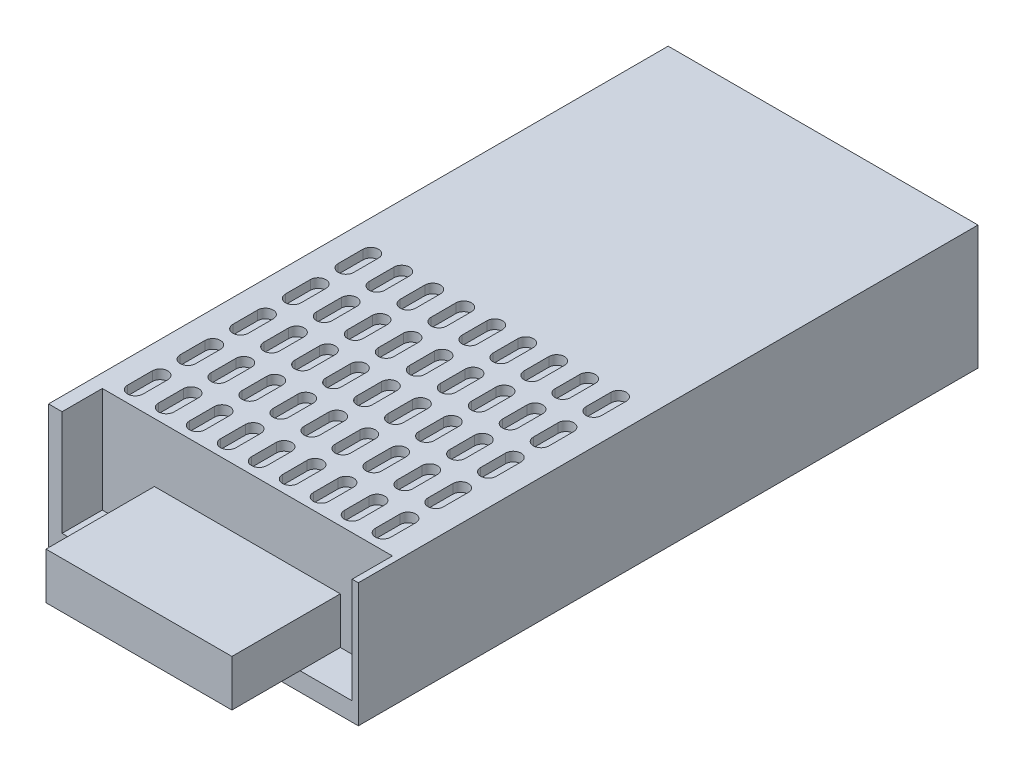
SolidWorks part; units mm, degrees
ref_plane "Front Plane" through (0, 0, 0) normal (0, 0, 1) x (1, 0, 0)
ref_plane "Top Plane" through (0, 0, 0) normal (0, 1, 0) x (1, 0, 0)
ref_plane "Right Plane" through (0, 0, 0) normal (1, 0, 0) x (0, 0, -1)
sketch "Sketch1" plane through (0, 0, 0) normal (0, 0, 1) x (1, 0, 0)
  line L1 (0, 0) -> (100, 0)
  line L2 (0, 0) -> (0, 40)
  line L3 (0, 40) -> (100, 40)
  line L4 (100, 0) -> (100, 40)
  dimension "D1" = 100
  dimension "D2" = 40
extrude "Boss-Extrude1" add sketch "Sketch1" along normal blind 200
sketch "Sketch2" plane through (0, 40, 0) normal (0, 1, 0) x (1, 0, 0)
  line L0 (100, -200) -> (0, -200) construction
  line L1 (4.3642, -200) -> (98, -200)
  line L2 (4.3642, -200) -> (4.3642, -187)
  line L3 (4.3642, -187) -> (98, -187)
  line L4 (98, -200) -> (98, -187)
  line L5 (100, -200) -> (100, 0) construction
  dimension "D1" = 13
  dimension "D2" = 2
extrude "Cut-Extrude1" cut sketch "Sketch2" against normal blind 34
sketch "Sketch3" plane through (0, 0, 187) normal (0, 0, 1) x (1, 0, 0)
  line L0 (98, 6) -> (4.3642, 6) construction
  line L1 (21.1821, 6) -> (81.1821, 6)
  line L2 (21.1821, 6) -> (21.1821, 21)
  line L3 (21.1821, 21) -> (81.1821, 21)
  line L4 (81.1821, 6) -> (81.1821, 21)
  line L5 (4.3642, 6) -> (98, 6) construction
  point P8 (51.1821, 6)
  point P9 (51.1821, 6)
  dimension "D1" = 60
  dimension "D2" = 15
extrude "Boss-Extrude2" add sketch "Sketch3" along normal blind 35
sketch "Sketch4" plane through (0, 40, 0) normal (0, 1, 0) x (1, 0, 0)
  line L0 (0, -200) -> (0, 0) construction
  line L2 (7.5, -174) -> (7.5, -182)
  line L4 (12.5, -174) -> (12.5, -182)
  line L5 (98, -187) -> (4.3642, -187) construction
  line L6 (17.5, -174) -> (17.5, -182)
  line L7 (22.5, -174) -> (22.5, -182)
  line L8 (27.5, -174) -> (27.5, -182)
  line L9 (32.5, -174) -> (32.5, -182)
  line L10 (37.5, -174) -> (37.5, -182)
  line L11 (42.5, -174) -> (42.5, -182)
  line L12 (47.5, -174) -> (47.5, -182)
  line L13 (52.5, -174) -> (52.5, -182)
  line L14 (57.5, -174) -> (57.5, -182)
  line L15 (62.5, -174) -> (62.5, -182)
  line L16 (67.5, -174) -> (67.5, -182)
  line L17 (72.5, -174) -> (72.5, -182)
  line L18 (77.5, -174) -> (77.5, -182)
  line L19 (82.5, -174) -> (82.5, -182)
  line L20 (87.5, -174) -> (87.5, -182)
  line L21 (92.5, -174) -> (92.5, -182)
  line L22 (17.5, -157) -> (17.5, -165)
  line L23 (22.5, -157) -> (22.5, -165)
  line L24 (27.5, -157) -> (27.5, -165)
  line L25 (32.5, -157) -> (32.5, -165)
  line L26 (37.5, -157) -> (37.5, -165)
  line L27 (42.5, -157) -> (42.5, -165)
  line L28 (47.5, -157) -> (47.5, -165)
  line L29 (52.5, -157) -> (52.5, -165)
  line L30 (57.5, -157) -> (57.5, -165)
  line L31 (62.5, -157) -> (62.5, -165)
  line L32 (67.5, -157) -> (67.5, -165)
  line L33 (72.5, -157) -> (72.5, -165)
  line L34 (77.5, -157) -> (77.5, -165)
  line L35 (82.5, -157) -> (82.5, -165)
  line L36 (87.5, -157) -> (87.5, -165)
  line L37 (92.5, -157) -> (92.5, -165)
  line L38 (17.5, -140) -> (17.5, -148)
  line L39 (22.5, -140) -> (22.5, -148)
  line L40 (27.5, -140) -> (27.5, -148)
  line L41 (32.5, -140) -> (32.5, -148)
  line L42 (37.5, -140) -> (37.5, -148)
  line L43 (42.5, -140) -> (42.5, -148)
  line L44 (47.5, -140) -> (47.5, -148)
  line L45 (52.5, -140) -> (52.5, -148)
  line L46 (57.5, -140) -> (57.5, -148)
  line L47 (62.5, -140) -> (62.5, -148)
  line L48 (67.5, -140) -> (67.5, -148)
  line L49 (72.5, -140) -> (72.5, -148)
  line L50 (77.5, -140) -> (77.5, -148)
  line L51 (82.5, -140) -> (82.5, -148)
  line L52 (87.5, -140) -> (87.5, -148)
  line L53 (92.5, -140) -> (92.5, -148)
  line L54 (17.5, -123) -> (17.5, -131)
  line L55 (22.5, -123) -> (22.5, -131)
  line L56 (27.5, -123) -> (27.5, -131)
  line L57 (32.5, -123) -> (32.5, -131)
  line L58 (37.5, -123) -> (37.5, -131)
  line L59 (42.5, -123) -> (42.5, -131)
  line L60 (47.5, -123) -> (47.5, -131)
  line L61 (52.5, -123) -> (52.5, -131)
  line L62 (57.5, -123) -> (57.5, -131)
  line L63 (62.5, -123) -> (62.5, -131)
  line L64 (67.5, -123) -> (67.5, -131)
  line L65 (72.5, -123) -> (72.5, -131)
  line L66 (77.5, -123) -> (77.5, -131)
  line L67 (82.5, -123) -> (82.5, -131)
  line L68 (87.5, -123) -> (87.5, -131)
  line L69 (92.5, -123) -> (92.5, -131)
  line L70 (17.5, -106) -> (17.5, -114)
  line L71 (22.5, -106) -> (22.5, -114)
  line L72 (27.5, -106) -> (27.5, -114)
  line L73 (32.5, -106) -> (32.5, -114)
  line L74 (37.5, -106) -> (37.5, -114)
  line L75 (42.5, -106) -> (42.5, -114)
  line L76 (47.5, -106) -> (47.5, -114)
  line L77 (52.5, -106) -> (52.5, -114)
  line L78 (57.5, -106) -> (57.5, -114)
  line L79 (62.5, -106) -> (62.5, -114)
  line L80 (67.5, -106) -> (67.5, -114)
  line L81 (72.5, -106) -> (72.5, -114)
  line L82 (77.5, -106) -> (77.5, -114)
  line L83 (82.5, -106) -> (82.5, -114)
  line L84 (87.5, -106) -> (87.5, -114)
  line L85 (92.5, -106) -> (92.5, -114)
  line L86 (7.5, -157) -> (7.5, -165)
  line L87 (12.5, -157) -> (12.5, -165)
  line L88 (7.5, -140) -> (7.5, -148)
  line L89 (12.5, -140) -> (12.5, -148)
  line L90 (7.5, -123) -> (7.5, -131)
  line L91 (12.5, -123) -> (12.5, -131)
  line L92 (7.5, -106) -> (7.5, -114)
  line L93 (12.5, -106) -> (12.5, -114)
  arc A0 (12.5, -174) -> (7.5, -174) centre (10, -174) ccw
  arc A1 (7.5, -182) -> (12.5, -182) centre (10, -182) ccw
  arc A2 (22.5, -174) -> (17.5, -174) centre (20, -174) ccw
  arc A3 (17.5, -182) -> (22.5, -182) centre (20, -182) ccw
  arc A4 (32.5, -174) -> (27.5, -174) centre (30, -174) ccw
  arc A5 (27.5, -182) -> (32.5, -182) centre (30, -182) ccw
  arc A6 (42.5, -174) -> (37.5, -174) centre (40, -174) ccw
  arc A7 (37.5, -182) -> (42.5, -182) centre (40, -182) ccw
  arc A8 (52.5, -174) -> (47.5, -174) centre (50, -174) ccw
  arc A9 (47.5, -182) -> (52.5, -182) centre (50, -182) ccw
  arc A10 (62.5, -174) -> (57.5, -174) centre (60, -174) ccw
  arc A11 (57.5, -182) -> (62.5, -182) centre (60, -182) ccw
  arc A12 (72.5, -174) -> (67.5, -174) centre (70, -174) ccw
  arc A13 (67.5, -182) -> (72.5, -182) centre (70, -182) ccw
  arc A14 (82.5, -174) -> (77.5, -174) centre (80, -174) ccw
  arc A15 (77.5, -182) -> (82.5, -182) centre (80, -182) ccw
  arc A16 (92.5, -174) -> (87.5, -174) centre (90, -174) ccw
  arc A17 (87.5, -182) -> (92.5, -182) centre (90, -182) ccw
  arc A18 (22.5, -157) -> (17.5, -157) centre (20, -157) ccw
  arc A19 (17.5, -165) -> (22.5, -165) centre (20, -165) ccw
  arc A20 (32.5, -157) -> (27.5, -157) centre (30, -157) ccw
  arc A21 (27.5, -165) -> (32.5, -165) centre (30, -165) ccw
  arc A22 (42.5, -157) -> (37.5, -157) centre (40, -157) ccw
  arc A23 (37.5, -165) -> (42.5, -165) centre (40, -165) ccw
  arc A24 (52.5, -157) -> (47.5, -157) centre (50, -157) ccw
  arc A25 (47.5, -165) -> (52.5, -165) centre (50, -165) ccw
  arc A26 (62.5, -157) -> (57.5, -157) centre (60, -157) ccw
  arc A27 (57.5, -165) -> (62.5, -165) centre (60, -165) ccw
  arc A28 (72.5, -157) -> (67.5, -157) centre (70, -157) ccw
  arc A29 (67.5, -165) -> (72.5, -165) centre (70, -165) ccw
  arc A30 (82.5, -157) -> (77.5, -157) centre (80, -157) ccw
  arc A31 (77.5, -165) -> (82.5, -165) centre (80, -165) ccw
  arc A32 (92.5, -157) -> (87.5, -157) centre (90, -157) ccw
  arc A33 (87.5, -165) -> (92.5, -165) centre (90, -165) ccw
  arc A34 (22.5, -140) -> (17.5, -140) centre (20, -140) ccw
  arc A35 (17.5, -148) -> (22.5, -148) centre (20, -148) ccw
  arc A36 (32.5, -140) -> (27.5, -140) centre (30, -140) ccw
  arc A37 (27.5, -148) -> (32.5, -148) centre (30, -148) ccw
  arc A38 (42.5, -140) -> (37.5, -140) centre (40, -140) ccw
  arc A39 (37.5, -148) -> (42.5, -148) centre (40, -148) ccw
  arc A40 (52.5, -140) -> (47.5, -140) centre (50, -140) ccw
  arc A41 (47.5, -148) -> (52.5, -148) centre (50, -148) ccw
  arc A42 (62.5, -140) -> (57.5, -140) centre (60, -140) ccw
  arc A43 (57.5, -148) -> (62.5, -148) centre (60, -148) ccw
  arc A44 (72.5, -140) -> (67.5, -140) centre (70, -140) ccw
  arc A45 (67.5, -148) -> (72.5, -148) centre (70, -148) ccw
  arc A46 (82.5, -140) -> (77.5, -140) centre (80, -140) ccw
  arc A47 (77.5, -148) -> (82.5, -148) centre (80, -148) ccw
  arc A48 (92.5, -140) -> (87.5, -140) centre (90, -140) ccw
  arc A49 (87.5, -148) -> (92.5, -148) centre (90, -148) ccw
  arc A50 (22.5, -123) -> (17.5, -123) centre (20, -123) ccw
  arc A51 (17.5, -131) -> (22.5, -131) centre (20, -131) ccw
  arc A52 (32.5, -123) -> (27.5, -123) centre (30, -123) ccw
  arc A53 (27.5, -131) -> (32.5, -131) centre (30, -131) ccw
  arc A54 (42.5, -123) -> (37.5, -123) centre (40, -123) ccw
  arc A55 (37.5, -131) -> (42.5, -131) centre (40, -131) ccw
  arc A56 (52.5, -123) -> (47.5, -123) centre (50, -123) ccw
  arc A57 (47.5, -131) -> (52.5, -131) centre (50, -131) ccw
  arc A58 (62.5, -123) -> (57.5, -123) centre (60, -123) ccw
  arc A59 (57.5, -131) -> (62.5, -131) centre (60, -131) ccw
  arc A60 (72.5, -123) -> (67.5, -123) centre (70, -123) ccw
  arc A61 (67.5, -131) -> (72.5, -131) centre (70, -131) ccw
  arc A62 (82.5, -123) -> (77.5, -123) centre (80, -123) ccw
  arc A63 (77.5, -131) -> (82.5, -131) centre (80, -131) ccw
  arc A64 (92.5, -123) -> (87.5, -123) centre (90, -123) ccw
  arc A65 (87.5, -131) -> (92.5, -131) centre (90, -131) ccw
  arc A66 (22.5, -106) -> (17.5, -106) centre (20, -106) ccw
  arc A67 (17.5, -114) -> (22.5, -114) centre (20, -114) ccw
  arc A68 (32.5, -106) -> (27.5, -106) centre (30, -106) ccw
  arc A69 (27.5, -114) -> (32.5, -114) centre (30, -114) ccw
  arc A70 (42.5, -106) -> (37.5, -106) centre (40, -106) ccw
  arc A71 (37.5, -114) -> (42.5, -114) centre (40, -114) ccw
  arc A72 (52.5, -106) -> (47.5, -106) centre (50, -106) ccw
  arc A73 (47.5, -114) -> (52.5, -114) centre (50, -114) ccw
  arc A74 (62.5, -106) -> (57.5, -106) centre (60, -106) ccw
  arc A75 (57.5, -114) -> (62.5, -114) centre (60, -114) ccw
  arc A76 (72.5, -106) -> (67.5, -106) centre (70, -106) ccw
  arc A77 (67.5, -114) -> (72.5, -114) centre (70, -114) ccw
  arc A78 (82.5, -106) -> (77.5, -106) centre (80, -106) ccw
  arc A79 (77.5, -114) -> (82.5, -114) centre (80, -114) ccw
  arc A80 (92.5, -106) -> (87.5, -106) centre (90, -106) ccw
  arc A81 (87.5, -114) -> (92.5, -114) centre (90, -114) ccw
  arc A82 (12.5, -157) -> (7.5, -157) centre (10, -157) ccw
  arc A83 (7.5, -165) -> (12.5, -165) centre (10, -165) ccw
  arc A84 (12.5, -140) -> (7.5, -140) centre (10, -140) ccw
  arc A85 (7.5, -148) -> (12.5, -148) centre (10, -148) ccw
  arc A86 (12.5, -123) -> (7.5, -123) centre (10, -123) ccw
  arc A87 (7.5, -131) -> (12.5, -131) centre (10, -131) ccw
  arc A88 (12.5, -106) -> (7.5, -106) centre (10, -106) ccw
  arc A89 (7.5, -114) -> (12.5, -114) centre (10, -114) ccw
  dimension "D1" = 8
  dimension "D2" = 5
  dimension "D3" = 10
  dimension "D4" = 5
  dimension "D5" = 9
  dimension "D6" = 5
extrude "Cut-Extrude2" cut sketch "Sketch4" against normal blind 3
